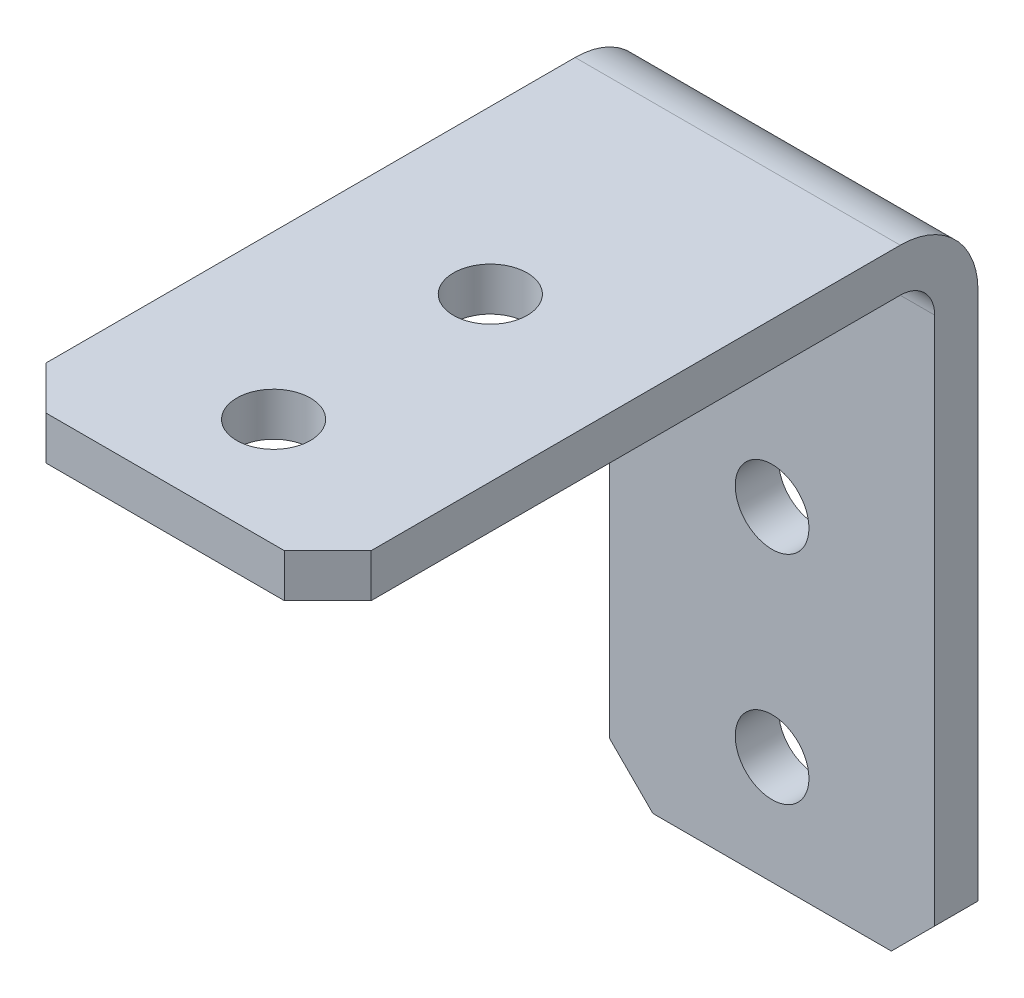
SolidWorks part; units mm, degrees
ref_plane "Front Plane" through (0, 0, 0) normal (0, 0, 1) x (1, 0, 0)
ref_plane "Top Plane" through (0, 0, 0) normal (0, 1, 0) x (1, 0, 0)
ref_plane "Right Plane" through (0, 0, 0) normal (1, 0, 0) x (0, 0, -1)
ref_plane "Plane1" through (-7.5, 0, 0) normal (-1, 0, 0) x (0, -1, 0)
sketch "Sketch1" plane through (-7.5, 0, 0) normal (-1, 0, 0) x (0, -1, 0)
  line L0 (15, -2) -> (15, 28)
  line L1 (15, 28) -> (-15, 28)
  line L2 (-15, 28) -> (-15, -2)
  line L3 (-15, -2) -> (15, -2)
extrude "Boss-Extrude1" add sketch "Sketch1" against normal blind 15
sketch "Sketch2" plane through (7.5, 0, 0) normal (1, 0, 0) x (0, 0, -1)
  line L0 (0, 13) -> (-28, 13)
  line L1 (-28, 13) -> (-28, -15)
  line L2 (-28, -15) -> (0, -15)
  line L3 (0, -15) -> (0, 13)
extrude "Cut-Extrude1" cut sketch "Sketch2" against normal through all
hole_wizard "Ø3.4 (3.4) Diameter Hole1" positions "Sketch4" profile "Sketch3" hole size "Ø3.4" standard "ANSI Metric"
sketch "Sketch4" plane through (0, 0, 0) normal (0, 0, 1) x (1, 0, 0)
  point P0 (0, 0)
  point P1 (0, -10)
sketch "Sketch3" plane through (0, 0, 0) normal (1, 0, 0) x (0, -1, 0)
  line L0 (0, 0) -> (0, 2)
  line L1 (0, 2) -> (1.7, 2)
  line L2 (1.7, 2) -> (1.7, 0)
  line L5 (1.7, 0) -> (0, 0)
  line L11 (0, -6.35) -> (0, 107.95) construction
  dimension "Thru Hole Dia." = 3.4
  dimension "Thru Hole Depth" = 2
hole_wizard "Ø3.4 (3.4) Diameter Hole2" positions "Sketch6" profile "Sketch5" hole size "Ø3.4" standard "ANSI Metric"
sketch "Sketch6" plane through (0, 13, 0) normal (0, -1, 0) x (-1, 0, 0)
  point P0 (0, -13)
  point P1 (0, -23)
sketch "Sketch5" plane through (0, 13, 13) normal (1, 0, 0) x (0, 0, -1)
  line L0 (0, 0) -> (0, 2)
  line L1 (0, 2) -> (1.7, 2)
  line L2 (1.7, 2) -> (1.7, 0)
  line L5 (1.7, 0) -> (0, 0)
  line L11 (0, -6.35) -> (0, 107.95) construction
  dimension "Thru Hole Dia." = 3.4
  dimension "Thru Hole Depth" = 2
chamfer "Chamfer1" distance 2 angle 45 4 edges at (7.5, -15, -1) (-7.5, 14, 28) (7.5, 14, 28) (-7.5, -15, -1)
fillet "Fillet1" radius 1.5875 1 edges at (0, 13, 0)
fillet "Fillet2" radius 3.5875 1 edges at (0, 15, -2)
